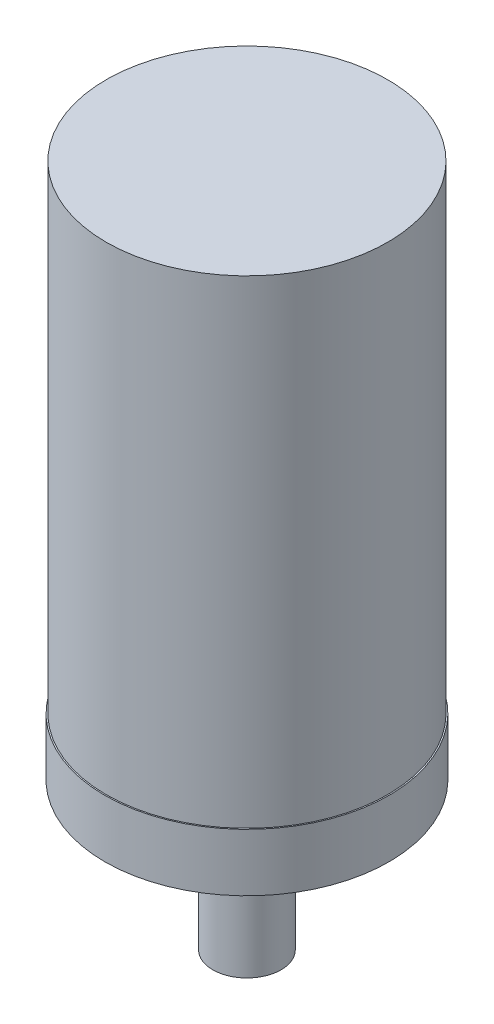
SolidWorks part; units mm, degrees
ref_plane "Alzado" through (0, 0, 0) normal (0, 0, 1) x (1, 0, 0)
ref_plane "Planta" through (0, 0, 0) normal (0, 1, 0) x (1, 0, 0)
ref_plane "Vista lateral" through (0, 0, 0) normal (1, 0, 0) x (0, 0, -1)
sketch "Croquis1" plane through (0, 0, 0) normal (0, 1, 0) x (1, 0, 0)
  circle A0 centre (0, 0) radius 9.5
  circle A1 centre (0, 0) radius 8.2
  dimension "D1" = 19
  dimension "D2" = 1.3
extrude "Saliente-Extruir1" add sketch "Croquis1" along normal blind 35
sketch "Croquis2" plane through (0, 0, 0) normal (0, 0, 1) x (1, 0, 0)
  line L0 (-9.5, 35) -> (-39.5, 41)
  line L1 (-39.5, 41) -> (-39.5, 57)
  line L2 (-39.5, 57) -> (-38.2, 57)
  line L3 (-38.2, 57) -> (-38.2, 42.0657)
  line L4 (-38.2, 42.0657) -> (-8.2, 36.0657)
  line L5 (-8.2, 36.0657) -> (-8.2, 35)
  line L6 (9.5, 35) -> (-9.5, 35) construction
  line L7 (-8.2, 35) -> (-9.5, 35)
  line L8 (0, 35) -> (0, 24.794) construction
  dimension "D1" = 30
  dimension "D2" = 22
  dimension "D3" = 6
  dimension "D4" = 1.3
  dimension "D5" = 1.3
  dimension "D6" = 1.3
revolve "Revolución1" add sketch "Croquis2" angle 360 about L8
sketch "Croquis3" plane through (0, 57, 0) normal (0, 1, 0) x (1, 0, 0)
  circle A0 centre (0, 0) radius 38.2
  circle A1 centre (0, 0) radius 39.137
extrude "Saliente-Extruir2" add sketch "Croquis3" along normal blind 130
sketch "Croquis4" plane through (0, 187, 0) normal (0, 1, 0) x (1, 0, 0)
  circle A0 centre (0, 0) radius 39.137
extrude "Saliente-Extruir3" add sketch "Croquis4" along normal blind 3
